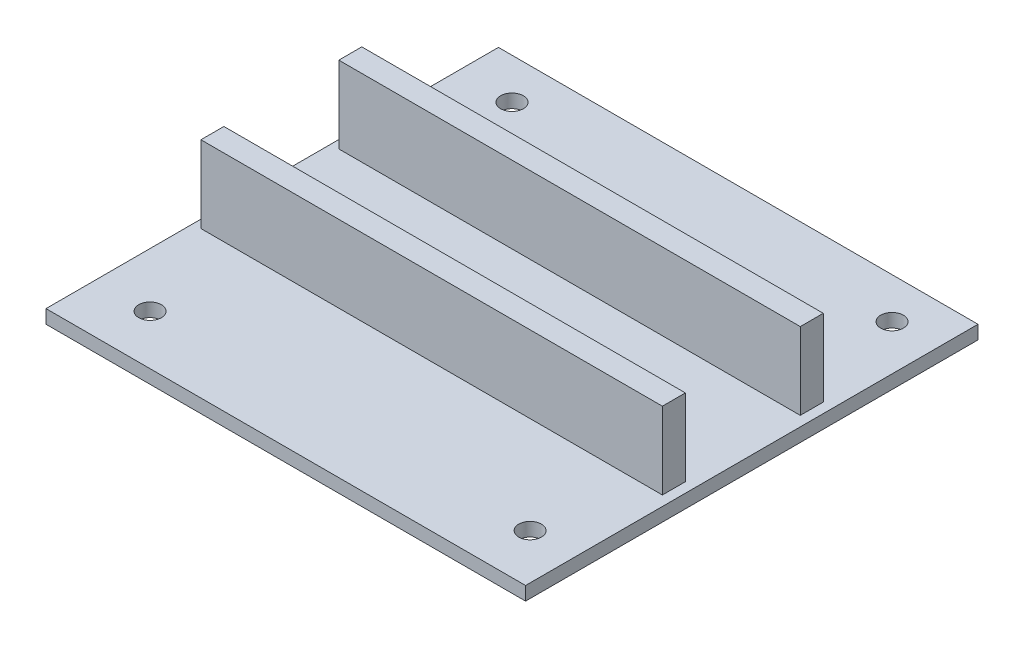
SolidWorks part; units mm, degrees
ref_plane "Piano frontale" through (0, 0, 0) normal (0, 0, 1) x (1, 0, 0)
ref_plane "Piano superiore" through (0, 0, 0) normal (0, 1, 0) x (1, 0, 0)
ref_plane "Piano destro" through (0, 0, 0) normal (1, 0, 0) x (0, 0, -1)
sketch "Schizzo1" plane through (0, 0, 0) normal (0, 1, 0) x (1, 0, 0)
  line L1 (26.5, 25) -> (-26.5, 25)
  line L2 (26.5, 25) -> (26.5, -25)
  line L3 (26.5, -25) -> (-26.5, -25)
  line L4 (-26.5, 25) -> (-26.5, -25)
  line L5 (26.5, 25) -> (-26.5, -25) construction
  line L6 (26.5, -25) -> (-26.5, 25) construction
  point P0 (0, 0)
  dimension "D1" = 53
  dimension "D2" = 50
extrude "Estrusione-Estrusione1" add sketch "Schizzo1" along normal blind 1.5
sketch "Schizzo2" plane through (0, 1.5, 0) normal (0, 1, 0) x (1, 0, 0)
  line L0 (26.5, -25) -> (26.5, 25) construction
  line L1 (-25.6, 9) -> (25.4, 9)
  line L2 (-25.6, 9) -> (-25.6, 6.46)
  line L3 (-25.6, 6.46) -> (25.4, 6.46)
  line L4 (25.4, 9) -> (25.4, 6.46)
  line L5 (26.5, 25) -> (-26.5, 25) construction
  line L7 (-25.6, -6.24) -> (25.4, -6.24)
  line L8 (-25.6, -6.24) -> (-25.6, -8.78)
  line L9 (-25.6, -8.78) -> (25.4, -8.78)
  line L10 (25.4, -6.24) -> (25.4, -8.78)
  dimension "D1" = 2.54
  dimension "D2" = 51
  dimension "D3" = 1.1
  dimension "D4" = 16
  dimension "D5" = 2.54
  dimension "D6" = 17.78
extrude "Estrusione-Estrusione2" add sketch "Schizzo2" along normal blind 8.5
sketch "Schizzo3" plane through (0, 1.5, 0) normal (0, 1, 0) x (1, 0, 0)
  line L0 (26.5, -25) -> (26.5, 25) construction
  line L1 (26.5, 25) -> (-26.5, 25) construction
  circle A0 centre (21.5, 20.5) radius 1.25
  circle A1 centre (-20.5, 20.5) radius 1.25
  circle A2 centre (21.5, -19.5) radius 1.25
  circle A3 centre (-20.5, -19.5) radius 1.25
  dimension "D1" = 2.5
  dimension "D4" = 2.5
  dimension "D6" = 2.5
  dimension "D8" = 2.5
  dimension "D2" = 5
  dimension "D3" = 4.5
  dimension "D5" = 42
  dimension "D7" = 40
extrude "Taglio-Estrusione1" cut sketch "Schizzo3" against normal blind 8.5
